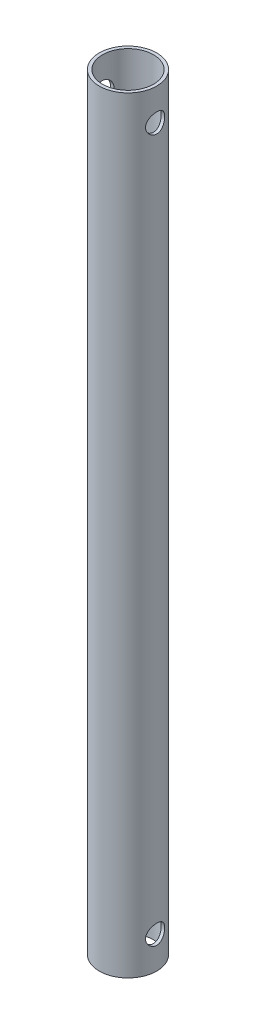
SolidWorks part; units mm, degrees
ref_plane "Alzado" through (0, 0, 0) normal (0, 0, 1) x (1, 0, 0)
ref_plane "Planta" through (0, 0, 0) normal (0, 1, 0) x (1, 0, 0)
ref_plane "Vista lateral" through (0, 0, 0) normal (1, 0, 0) x (0, 0, -1)
sketch "Croquis1" plane through (0, 0, 0) normal (0, 1, 0) x (1, 0, 0)
  circle A0 centre (0, 0) radius 4
  circle A1 centre (0, 0) radius 4.5
  dimension "D1" = 9
  dimension "D2" = 8
extrude "Saliente-Extruir1" add sketch "Croquis1" along normal blind 120
sketch "Croquis2" plane through (0, 0, 0) normal (1, 0, 0) x (0, 0, -1)
  line L0 (0, 0) -> (0, 5) construction
  line L1 (0, 5) -> (0, 115) construction
  line L2 (0, 115) -> (0, 120) construction
  line L3 (4.5, 120) -> (-4.5, 120) construction
  circle A0 centre (0, 115) radius 1.5
  circle A1 centre (0, 5) radius 1.5
  dimension "D3" = 3
  dimension "D1" = 5
  dimension "D2" = 5
extrude "Cortar-Extruir1" cut sketch "Croquis2" against normal through all and the other way through all
